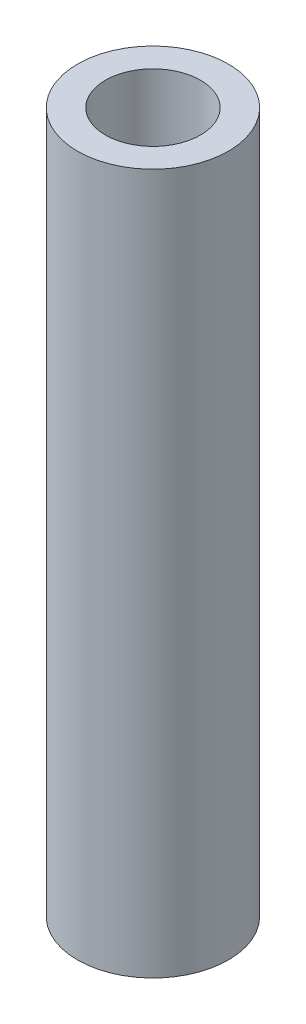
SolidWorks part; units mm, degrees
material "6061-T6 (SS)"
ref_plane "X-Y Datum" through (0, 0, 0) normal (0, 0, 1) x (1, 0, 0)
ref_plane "X-Z Datum" through (0, 0, 0) normal (0, 1, 0) x (1, 0, 0)
ref_plane "Y-Z Datum" through (0, 0, 0) normal (1, 0, 0) x (0, 0, -1)
sketch "Sketch1" plane through (0, 0, 0) normal (0, 1, 0) x (1, 0, 0)
  circle A0 centre (0, 0) radius 3.175
  circle A1 centre (0, 0) radius 2
  dimension "D1" = 6.35
  dimension "D2" = 4
extrude "Boss-Extrude1" add sketch "Sketch1" against normal blind 29.464
